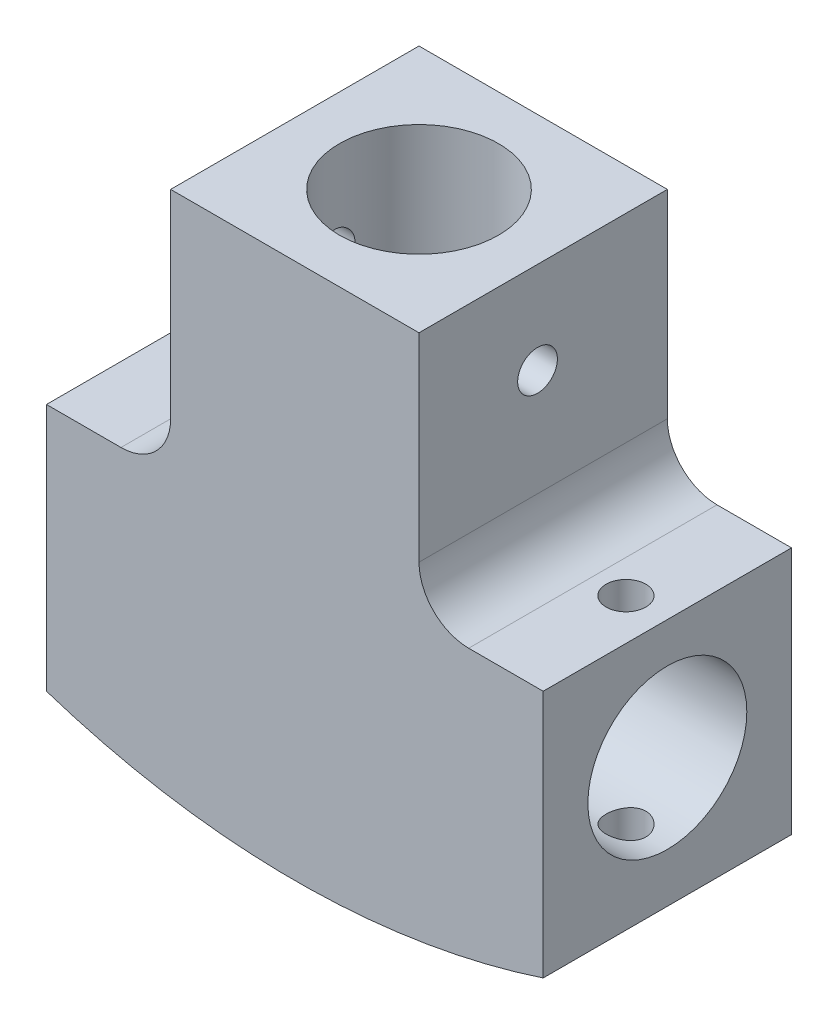
SolidWorks part; units mm, degrees
ref_plane "Alzado" through (0, 0, 0) normal (0, 0, 1) x (1, 0, 0)
ref_plane "Planta" through (0, 0, 0) normal (0, 1, 0) x (1, 0, 0)
ref_plane "Vista lateral" through (0, 0, 0) normal (1, 0, 0) x (0, 0, -1)
sketch "Croquis2" plane through (0, 0, 0) normal (0, 1, 0) x (1, 0, 0)
  line L1 (-25, -12.5) -> (25, -12.5)
  line L2 (-25, -12.5) -> (-25, 12.5)
  line L3 (-25, 12.5) -> (25, 12.5)
  line L4 (25, -12.5) -> (25, 12.5)
  line L5 (-25, -12.5) -> (25, 12.5) construction
  line L6 (-25, 12.5) -> (25, -12.5) construction
  point P0 (0, 0)
  dimension "D1" = 50
  dimension "D2" = 25
extrude "Saliente-Extruir2" add sketch "Croquis2" along normal blind 25
sketch "Croquis9" plane through (0, 0, 0) normal (0, 1, 0) x (1, 0, 0)
  line L1 (-12.5, -12.5) -> (12.5, -12.5)
  line L2 (-12.5, -12.5) -> (-12.5, 12.5)
  line L3 (-12.5, 12.5) -> (12.5, 12.5)
  line L4 (12.5, -12.5) -> (12.5, 12.5)
  line L5 (-12.5, -12.5) -> (12.5, 12.5) construction
  line L6 (-12.5, 12.5) -> (12.5, -12.5) construction
  point P0 (0, 0)
  dimension "D1" = 25
  dimension "D2" = 25
extrude "Saliente-Extruir3" add sketch "Croquis9" along normal blind 50 contours L2 L1 L4 L3
sketch "Croquis10" plane through (0, 0, 0) normal (1, 0, 0) x (0, 0, -1)
  circle A0 centre (0, 12.9573) radius 8
  dimension "D1" = 16
extrude "Cortar-Extruir2" cut sketch "Croquis10" along normal blind 43 and the other way blind 49
sketch "Croquis11" plane through (0, 50, 0) normal (0, 1, 0) x (1, 0, 0)
  circle A0 centre (0, 0) radius 8
  dimension "D1" = 16
extrude "Cortar-Extruir3" cut sketch "Croquis11" against normal mid plane 75
fillet "Redondeo1" radius 5 2 edges at (-12.5, 25, 0) (12.5, 25, 0)
sketch "Croquis13" plane through (0, 0, 0) normal (0, 0, 1) x (1, 0, 0)
  line L0 (40.27, 0) -> (-33.9387, 0) construction
  line L1 (-25, 25) -> (-25, 0) construction
  line L2 (-25, 25) -> (-25, 0) construction
  line L3 (25, 25) -> (25, 0) construction
  line L4 (25, 25) -> (25, 0) construction
  line L5 (-25, 0) -> (25, 0)
  arc A0 (25, 0) -> (-25, 0) centre (0, 75.9934) cw
  dimension "D1" = 80
extrude "Saliente-Extruir4" add sketch "Croquis13" along normal mid plane 25
sketch "Croquis15" plane through (-12.5, 0, 0) normal (-1, 0, 0) x (0, 0, 1)
  circle A0 centre (0.5683, 40.7593) radius 2
  dimension "D1" = 4
extrude "Cortar-Extruir4" cut sketch "Croquis15" against normal blind 33
sketch "Croquis16" plane through (0, 25, 0) normal (0, 1, 0) x (1, 0, 0)
  circle A0 centre (20.8337, 0) radius 2
  dimension "D1" = 4
extrude "Cortar-Extruir5" cut sketch "Croquis16" against normal blind 33
mirror "Simetría1" about plane through (0, 0, 0) normal (1, 0, 0) of "Cortar-Extruir5"
